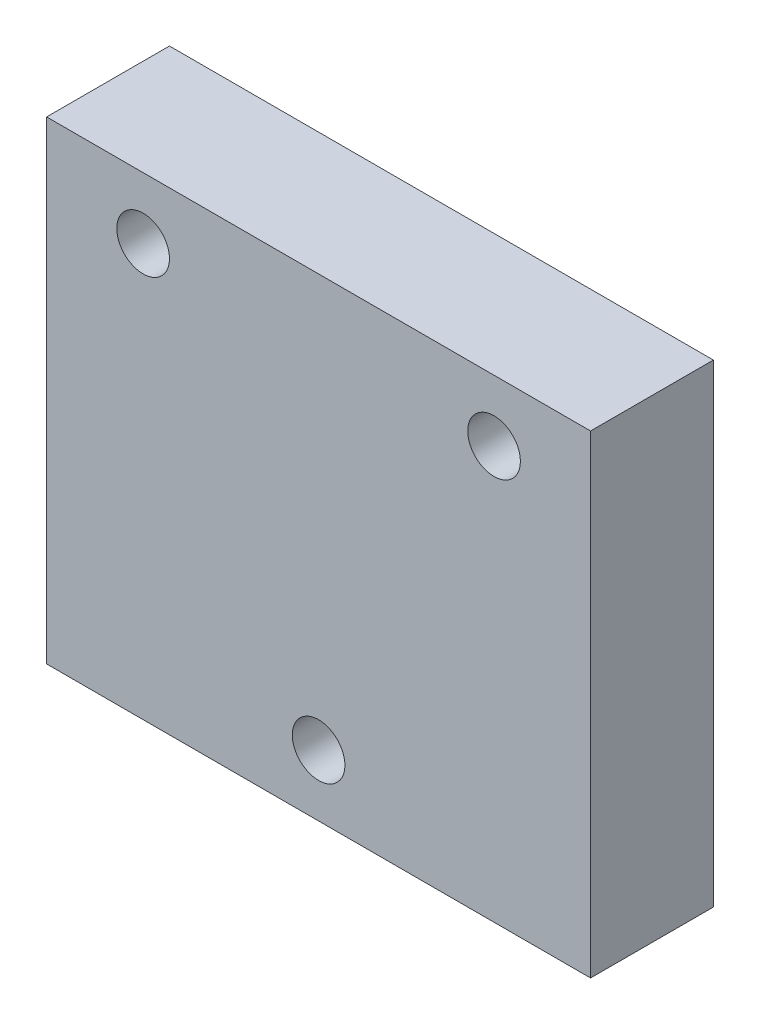
SolidWorks part; units mm, degrees
ref_plane "前视基准面" through (0, 0, 0) normal (0, 0, 1) x (1, 0, 0)
ref_plane "上视基准面" through (0, 0, 0) normal (0, 1, 0) x (1, 0, 0)
ref_plane "右视基准面" through (0, 0, 0) normal (1, 0, 0) x (0, 0, -1)
sketch "草图1" plane through (0, 0, 0) normal (0, 0, 1) x (1, 0, 0)
  line L1 (-15.5, 13.5) -> (15.5, 13.5)
  line L2 (-15.5, 13.5) -> (-15.5, -13.5)
  line L3 (-15.5, -13.5) -> (15.5, -13.5)
  line L4 (15.5, 13.5) -> (15.5, -13.5)
  line L5 (-15.5, 13.5) -> (15.5, -13.5) construction
  line L6 (-15.5, -13.5) -> (15.5, 13.5) construction
  point P0 (0, 0)
  dimension "D1" = 31
  dimension "D2" = 27
extrude "凸台-拉伸1" add sketch "草图1" along normal blind 7
sketch "草图2" plane through (0, 0, 7) normal (0, 0, 1) x (1, 0, 0)
  line L1 (-15.5, 13.5) -> (-15.5, -13.5) construction
  line L2 (15.5, 13.5) -> (-15.5, 13.5) construction
  circle A0 centre (-10, 10) radius 1.5
  circle A1 centre (10, 10) radius 1.5
  circle A2 centre (0, -10) radius 1.5
  point P6 (0, 0)
  point P7 (0, 0)
  point P8 (0, 0)
  point P11 (0, 0)
  dimension "D1" = 3
  dimension "D2" = 3
  dimension "D3" = 3
  dimension "D4" = 20
  dimension "D5" = 20
  dimension "D6" = 10
  dimension "D7" = 5.5
  dimension "D8" = 3.5
extrude "切除-拉伸1" cut sketch "草图2" against normal blind 7
